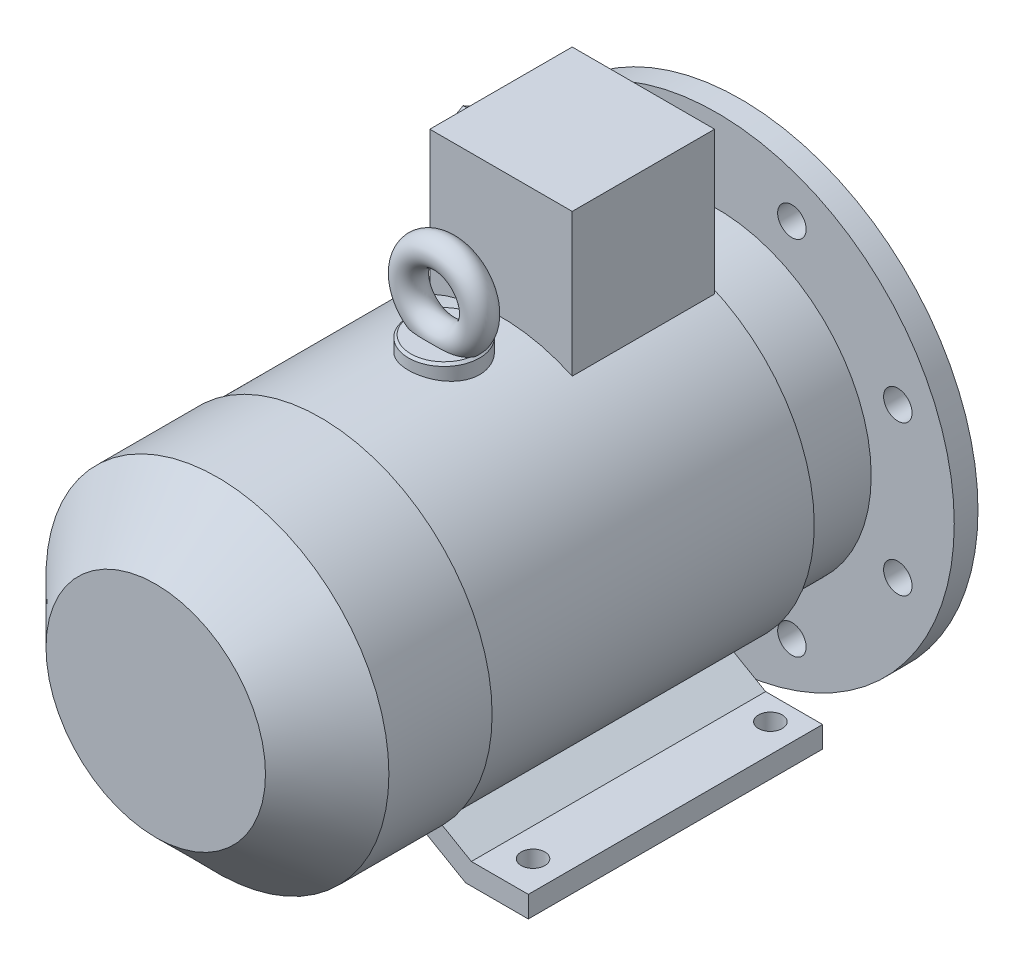
SolidWorks part; units mm, degrees
material "Ст.3 ГОСТ 380-88"
ref_plane "Спереди" through (0, 0, 0) normal (0, 0, 1) x (1, 0, 0)
ref_plane "Сверху" through (0, 0, 0) normal (0, 1, 0) x (1, 0, 0)
ref_plane "Справа" through (0, 0, 0) normal (1, 0, 0) x (0, 0, -1)
sketch "Эскиз1" plane through (0, 0, 0) normal (0, 0, 1) x (1, 0, 0)
  circle A0 centre (0, 0) radius 11
  dimension "D1" = 22
extrude "Вытянуть1" add sketch "Эскиз1" along normal blind 50
sketch "Эскиз2" plane through (0, 0, 0) normal (0, 0, -1) x (-1, 0, 0)
  line L0 (0, 0) -> (0, 12.6748) construction
  line L2 (-3, 13.5) -> (3, 13.5)
  line L3 (-3, 13.5) -> (-3, 7.5)
  line L4 (-3, 7.5) -> (3, 7.5)
  line L5 (3, 13.5) -> (3, 7.5)
  circle A1 centre (0, 0) radius 11 construction
  dimension "D1" = 6
  dimension "D2" = 6
  dimension "D3" = 24.5
extrude "Вытянуть2" add sketch "Эскиз2" against normal blind 25 and the other way blind 0.1
chamfer "Фаска1" distance 1 angle 45 1 edges at (0, -11, 0)
sketch "Эскиз3" plane through (0, 0, 50) normal (0, 0, 1) x (1, 0, 0)
  circle A0 centre (0, 0) radius 100
  dimension "D1" = 200
extrude "Вытянуть3" add sketch "Эскиз3" along normal blind 10
sketch "Эскиз4" plane through (0, 0, 50) normal (0, 0, -1) x (-1, 0, 0)
  circle A0 centre (0, 0) radius 65
  circle A1 centre (0, 0) radius 60
  dimension "D1" = 130
  dimension "D2" = 120
extrude "Вытянуть4" add sketch "Эскиз4" along normal blind 3.5
sketch "Эскиз5" plane through (0, 0, 50) normal (0, 0, -1) x (-1, 0, 0)
  circle A0 centre (0, 0) radius 60
  circle A1 centre (0, 0) radius 18
  dimension "D1" = 120
  dimension "D2" = 36
extrude "Вырез-Вытянуть1" cut sketch "Эскиз5" against normal blind 3.5
chamfer "Фаска2" distance 1 angle 45 2 edges at (-65, 0, 46.5) (-18, 0, 50)
sketch "Эскиз6" plane through (0, 0, 60) normal (0, 0, 1) x (1, 0, 0)
  circle A0 centre (0, 0) radius 65
  dimension "D1" = 130
extrude "Вытянуть5" add sketch "Эскиз6" along normal blind 30
sketch "Эскиз7" plane through (0, 0, 90) normal (0, 0, 1) x (1, 0, 0)
  circle A0 centre (0, 0) radius 71
  dimension "D1" = 142
extrude "Вытянуть6" add sketch "Эскиз7" along normal blind 137
sketch "Эскиз8" plane through (0, 0, 227) normal (0, 0, 1) x (1, 0, 0)
  circle A0 centre (0, 0) radius 72.2481
  dimension "D1" = 144.4962
extrude "Вытянуть7" add sketch "Эскиз8" along normal blind 69.5
chamfer "Фаска3" distance 26 angle 45 1 edges at (72.2481, 0, 296.5)
sketch "Эскиз9" plane through (0, 0, 50) normal (0, 0, -1) x (-1, 0, 0)
  line L0 (0, 0) -> (0, 120.2439) construction
  line L1 (0, 0) -> (-48.9872, 118.2656) construction
  circle A0 centre (-31.5714, 76.2201) radius 6
  circle A2 centre (31.5714, 76.2201) radius 6
  circle A3 centre (76.2201, 31.5714) radius 6
  circle A4 centre (76.2201, -31.5714) radius 6
  circle A5 centre (31.5714, -76.2201) radius 6
  circle A6 centre (-31.5714, -76.2201) radius 6
  circle A7 centre (-76.2201, -31.5714) radius 6
  circle A8 centre (-76.2201, 31.5714) radius 6
  dimension "D2" = 12
  dimension "D4" = 82.5
  dimension "D1" = 22.5
  dimension "D3" = 82.5
  dimension "D5" = 82.5
extrude "Вырез-Вытянуть2" cut sketch "Эскиз9" against normal through all
sketch "Эскиз10" plane through (0, 0, 90) normal (0, 0, -1) x (-1, 0, 0)
  line L0 (-74.5, -80) -> (-48.0885, -80)
  line L1 (-48.0885, -80) -> (-11.5155, -58.8846)
  line L2 (-11.5155, -58.8846) -> (-23.2951, -55.2932)
  line L3 (-23.2951, -55.2932) -> (-50.5, -71)
  line L4 (-50.5, -71) -> (-74.5, -71)
  line L5 (-74.5, -71) -> (-74.5, -80)
  line L6 (0, 0) -> (0, -117.9278) construction
  line L7 (74.5, -71) -> (74.5, -80)
  line L8 (50.5, -71) -> (74.5, -71)
  line L9 (74.5, -80) -> (48.0885, -80)
  line L10 (48.0885, -80) -> (11.5155, -58.8846)
  line L11 (11.5155, -58.8846) -> (23.2951, -55.2932)
  line L12 (23.2951, -55.2932) -> (50.5, -71)
  circle A0 centre (0, 0) radius 60 construction
  dimension "D1" = 9
  dimension "D2" = 74.5
  dimension "D3" = 24
  dimension "D4" = 9
  dimension "D5" = 60
  dimension "D6" = 80
extrude "Вытянуть8" add sketch "Эскиз10" against normal blind 124
sketch "Эскиз11" plane through (0, -80, 0) normal (0, -1, 0) x (1, 0, 0)
  line L0 (114.3491, 100) -> (-122.7539, 100) construction
  line L1 (0, 0) -> (0, 308.5542) construction
  line L2 (-62.5, 100) -> (62.5, 100) construction
  line L3 (-62.5, 100) -> (-62.5, 200) construction
  circle A0 centre (-62.5, 100) radius 5
  circle A1 centre (62.5, 100) radius 5
  circle A2 centre (-62.5, 200) radius 5
  circle A3 centre (62.5, 200) radius 5
  dimension "D2" = 10
  dimension "D1" = 100
  dimension "D3" = 62.5
  dimension "D4" = 90
  dimension "D5" = 200
  dimension "D6" = 100
  dimension "D7" = 125
extrude "Вырез-Вытянуть3" cut sketch "Эскиз11" against normal up to next
sketch "Эскиз12" plane through (0, 0, 0) normal (0, 1, 0) x (1, 0, 0)
  line L0 (0, 0) -> (0, -296.5) construction
  line L1 (-30, -91) -> (30, -91)
  line L2 (-30, -91) -> (-30, -151)
  line L3 (-30, -151) -> (30, -151)
  line L4 (30, -91) -> (30, -151)
  line L6 (-46.2481, -296.5) -> (46.2481, -296.5) construction
  line L8 (71, -90) -> (-71, -90) construction
  dimension "D1" = 60
  dimension "D2" = 1
  dimension "D3" = 60
extrude "Вытянуть9" add sketch "Эскиз12" along normal blind 124.5
sketch "Эскиз13" plane through (0, 0, 0) normal (0, 1, 0) x (1, 0, 0)
  line L0 (0, 0) -> (0, -227) construction
  line L1 (72.2481, -227) -> (-72.2481, -227) construction
  circle A0 centre (0, -175) radius 15
  dimension "D1" = 30
  dimension "D2" = 175
extrude "Вытянуть10" add sketch "Эскиз13" along normal blind 76.5
chamfer "Фаска4" distance 1 angle 45 1 edges at (0, 76.5, 190)
ref_plane "Плоскость1" through (0, 0, 175) normal (0, 0, 1) x (1, 0, 0)
sketch "Эскиз14" plane through (0, 0, 175) normal (0, 0, 1) x (1, 0, 0)
  line L0 (14, 76.5) -> (-14, 76.5) construction
  line L1 (0, 0) -> (0, 111.9091) construction
  line L2 (-70.1151, 113.5856) -> (-67.6125, 111.9091) construction
  circle A0 centre (0, 91.5) radius 15
  dimension "D1" = 30
sketch "Эскиз15" plane through (0, 0, 0) normal (1, 0, 0) x (0, 0, -1)
  line L1 (-175, 106.5) -> (-175, 76.5) construction
  circle A0 centre (-175, 106.5) radius 6
  dimension "D1" = 12
  dimension "D2" = 15
sweep "По траектории1" add profiles "Эскиз15" path "Эскиз14"
sketch "Эскиз16" plane through (-30, 0, 0) normal (-1, 0, 0) x (0, 0, 1)
  line L1 (91, 124.5) -> (91, 64.3506) construction
  line L2 (91, 124.5) -> (151, 124.5) construction
  circle A0 centre (121, 94.5) radius 8
  dimension "D1" = 16
  dimension "D2" = 30
  dimension "D3" = 30
extrude "Вытянуть11" add sketch "Эскиз16" along normal blind 6
sketch "Эскиз17" plane through (-36, 0, 0) normal (-1, 0, 0) x (0, 0, 1)
  line L1 (121, 110.0885) -> (107.5, 102.2942)
  line L2 (107.5, 102.2942) -> (107.5, 86.7058)
  line L3 (107.5, 86.7058) -> (121, 78.9115)
  line L4 (121, 78.9115) -> (134.5, 86.7058)
  line L5 (134.5, 86.7058) -> (134.5, 102.2942)
  line L6 (134.5, 102.2942) -> (121, 110.0885)
  line L7 (121, 94.5) -> (121, 137.7813) construction
  circle A0 centre (121, 94.5) radius 13.5 construction
  circle A1 centre (121, 94.5) radius 8 construction
  dimension "D1" = 27
extrude "Вытянуть12" add sketch "Эскиз17" along normal blind 10
sketch "Эскиз18" plane through (-46, 0, 0) normal (-1, 0, 0) x (0, 0, 1)
  circle A0 centre (121, 94.5) radius 6
  circle A1 centre (121, 94.5) radius 8 construction
  dimension "D1" = 12
extrude "Вырез-Вытянуть4" cut sketch "Эскиз18" against normal blind 10
